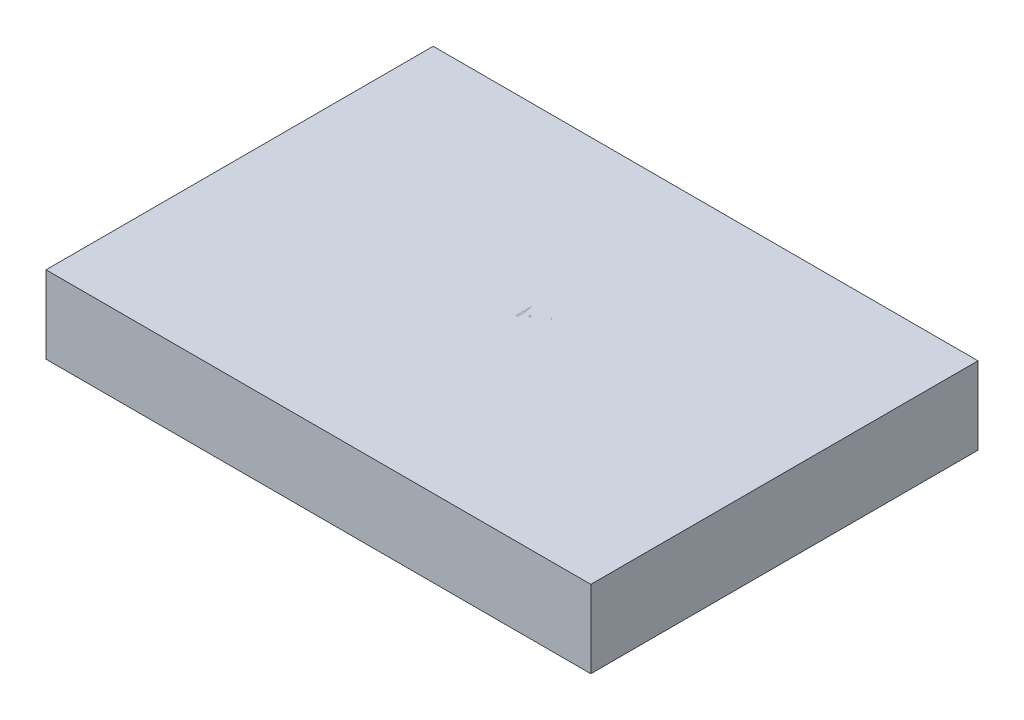
SolidWorks part; units mm, degrees
ref_plane "Front Plane" through (0, 0, 0) normal (0, 0, 1) x (1, 0, 0)
ref_plane "Top Plane" through (0, 0, 0) normal (0, 1, 0) x (1, 0, 0)
ref_plane "Right Plane" through (0, 0, 0) normal (1, 0, 0) x (0, 0, -1)
sketch "Sketch1" plane through (0, 0, 0) normal (0, 1, 0) x (1, 0, 0)
  line L1 (-50.038, -35.56) -> (50.038, -35.56)
  line L2 (-50.038, -35.56) -> (-50.038, 35.56)
  line L3 (-50.038, 35.56) -> (50.038, 35.56)
  line L4 (50.038, -35.56) -> (50.038, 35.56)
  line L5 (-50.038, -35.56) -> (50.038, 35.56) construction
  line L6 (-50.038, 35.56) -> (50.038, -35.56) construction
  point P0 (0, 0)
  dimension "D1" = 100.076
  dimension "D2" = 71.12
extrude "Boss-Extrude1" add sketch "Sketch1" along normal blind 14.224
sketch "Sketch3" plane through (0, 14.224, 0) normal (0, 1, 0) x (1, 0, 0)
  text T0 "BATTERY"
extrude "Boss-Extrude2" add sketch "Sketch3" against normal blind 0.1 separate body
